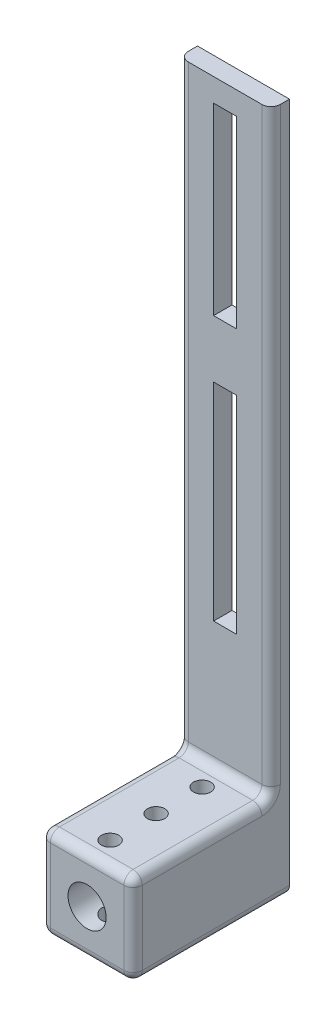
SolidWorks part; units mm, degrees
ref_plane "Alzado" through (0, 0, 0) normal (0, 0, 1) x (1, 0, 0)
ref_plane "Planta" through (0, 0, 0) normal (0, 1, 0) x (1, 0, 0)
ref_plane "Vista lateral" through (0, 0, 0) normal (1, 0, 0) x (0, 0, -1)
sketch "Croquis1" plane through (0, 0, 0) normal (0, 0, 1) x (1, 0, 0)
  line L1 (10, 0) -> (-10, 0)
  line L2 (10, 0) -> (10, 150)
  line L3 (10, 150) -> (-10, 150)
  line L4 (-10, 0) -> (-10, 150)
  line L5 (2.5, 105) -> (-2.5, 105)
  line L6 (2.5, 105) -> (2.5, 145)
  line L7 (2.5, 145) -> (-2.5, 145)
  line L8 (-2.5, 105) -> (-2.5, 145)
  line L9 (2.5, 105) -> (-2.5, 145) construction
  line L10 (2.5, 145) -> (-2.5, 105) construction
  line L11 (2.5, 47.5) -> (-2.5, 47.5)
  line L12 (2.5, 47.5) -> (2.5, 92.5)
  line L13 (2.5, 92.5) -> (-2.5, 92.5)
  line L14 (-2.5, 47.5) -> (-2.5, 92.5)
  line L15 (2.5, 47.5) -> (-2.5, 92.5) construction
  line L16 (2.5, 92.5) -> (-2.5, 47.5) construction
  circle A0 centre (0, 10) radius 4.15
  point P6 (0, 125)
  point P11 (0, 70)
  dimension "D3" = 10
  dimension "D1" = 10
  dimension "D2" = 150
  dimension "D4" = 0
  dimension "D5" = 25
  dimension "D6" = 80
extrude "Saliente-Extruir1" add sketch "Croquis1" along normal blind 4
sketch "Croquis2" plane through (0, 0, 0) normal (0, 0, 1) x (1, 0, 0)
  line L0 (10, 0) -> (10, 150) construction
  line L1 (-10, 0) -> (10, 0)
  line L2 (-10, 0) -> (-10, 20)
  line L3 (-10, 20) -> (10, 20)
  line L4 (10, 0) -> (10, 20)
  circle A0 centre (0, 10) radius 4.15
extrude "Saliente-Extruir2" add sketch "Croquis2" along normal blind 30 from surface at 4 starting at face at (0, 75, 4)
fillet "Redondeo1" radius 2 11 edges at (-10, 85, 4) (10, 85, 4) (0, 20, 4) (10, 20, 19) (-10, 20, 19) (-10, 0, 17) (10, 0, 17) (-10, 10, 34) (0, 20, 34) (10, 10, 34) (0, 0, 34)
sketch "Croquis3" plane through (0, 0, 0) normal (0, 1, 0) x (1, 0, 0)
  line L0 (8, -34) -> (-8, -34) construction
  line L1 (-8, -4) -> (8, -4) construction
  circle A0 centre (0, -9) radius 1.875
  circle A1 centre (0, -29) radius 1.875
  circle A2 centre (0, -19) radius 1.875
  dimension "D1" = 3.75
  dimension "D2" = 3.75
  dimension "D5" = 3.75
  dimension "D3" = 5
  dimension "D4" = 5
  dimension "D6" = 15
extrude "Cortar-Extruir1" cut sketch "Croquis3" along normal up to surface (20 mm away) from surface at 0 up to face at (0, 20, 19) starting at face at (0, 0, 16)
